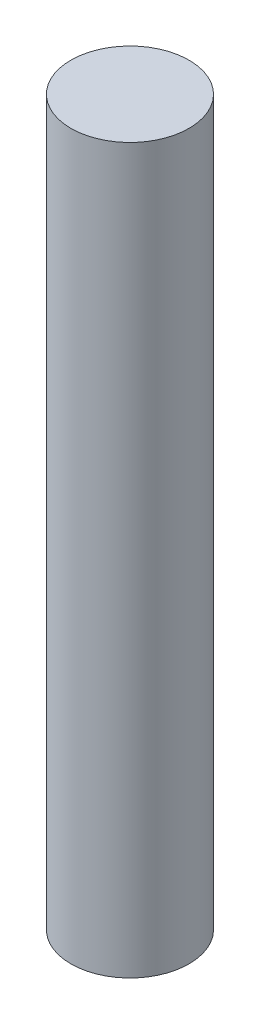
SolidWorks part; units mm, degrees
ref_plane "Front Plane" through (0, 0, 0) normal (0, 0, 1) x (1, 0, 0)
ref_plane "Top Plane" through (0, 0, 0) normal (0, 1, 0) x (1, 0, 0)
ref_plane "Right Plane" through (0, 0, 0) normal (1, 0, 0) x (0, 0, -1)
sketch "Sketch1" plane through (0, 0, 0) normal (0, 1, 0) x (1, 0, 0)
  circle A0 centre (0, 0) radius 0.245
  dimension "D1" = 0.49
extrude "Boss-Extrude1" add sketch "Sketch1" along normal blind 3
